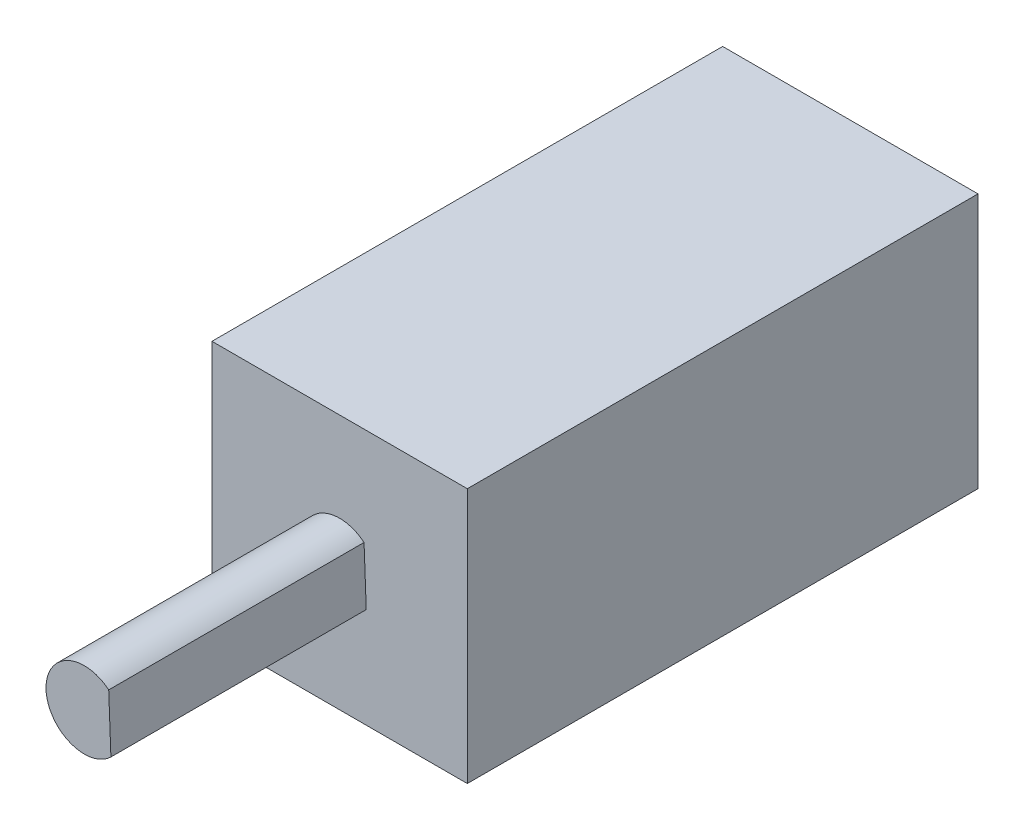
SolidWorks part; units mm, degrees
ref_plane "Front Plane" through (0, 0, 0) normal (0, 0, 1) x (1, 0, 0)
ref_plane "Top Plane" through (0, 0, 0) normal (0, 1, 0) x (1, 0, 0)
ref_plane "Right Plane" through (0, 0, 0) normal (1, 0, 0) x (0, 0, -1)
sketch "Sketch1" plane through (0, 0, 0) normal (0, 0, 1) x (1, 0, 0)
  line L1 (-5, 5) -> (5, 5)
  line L2 (-5, 5) -> (-5, -5)
  line L3 (-5, -5) -> (5, -5)
  line L4 (5, 5) -> (5, -5)
  line L5 (-5, 5) -> (5, -5) construction
  line L6 (-5, -5) -> (5, 5) construction
  point P0 (0, 0)
  dimension "D1" = 10
  dimension "D2" = 10
extrude "Boss-Extrude1" add sketch "Sketch1" along normal blind 20 contours L2 L1 L4 L3
sketch "Sketch2" plane through (0, 0, 20) normal (0, 0, 1) x (1, 0, 0)
  line L0 (0.9564, 1.1556) -> (1.0421, -1.0789)
  arc A0 (0.9564, 1.1556) -> (1.0421, -1.0789) centre (0, 0) ccw
  dimension "D1" = 1.5
  dimension "D2" = 1
extrude "Boss-Extrude2" add sketch "Sketch2" along normal blind 10
